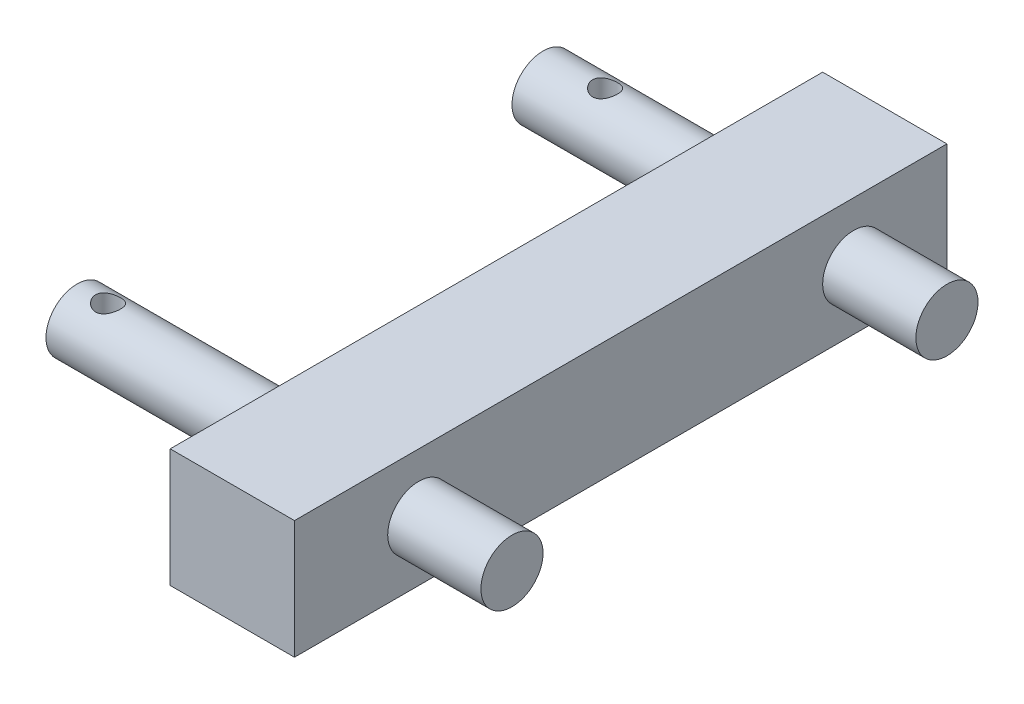
SolidWorks part; units mm, degrees
ref_plane "Front Plane" through (0, 0, 0) normal (0, 0, 1) x (1, 0, 0)
ref_plane "Top Plane" through (0, 0, 0) normal (0, 1, 0) x (1, 0, 0)
ref_plane "Right Plane" through (0, 0, 0) normal (1, 0, 0) x (0, 0, -1)
sketch "Sketch1" plane through (0, 0, 0) normal (1, 0, 0) x (0, 0, -1)
  line L1 (60, 94.9275) -> (-150, 94.9275)
  line L2 (60, 94.9275) -> (60, 56.8275)
  line L3 (60, 56.8275) -> (-150, 56.8275)
  line L4 (-150, 94.9275) -> (-150, 56.8275)
  dimension "D1" = 210
  dimension "D2" = 38.1
extrude "Boss-Extrude1" add sketch "Sketch1" along normal blind 40
sketch "Sketch2" plane through (40, 0, 0) normal (1, 0, 0) x (0, 0, -1)
  line L0 (-150, 56.8275) -> (60, 56.8275) construction
  line L2 (-150, 94.9275) -> (-150, 56.8275) construction
  circle A0 centre (30, 75.8275) radius 10
  dimension "D1" = 180
  dimension "D2" = 20
  dimension "D4" = 19
sketch "Sketch4" plane through (40, 0, 0) normal (1, 0, 0) x (0, 0, -1)
  line L1 (-150, 94.9275) -> (-150, 56.8275) construction
  line L2 (-150, 56.8275) -> (60, 56.8275) construction
  circle A0 centre (-110, 75.8775) radius 10
  dimension "D2" = 20
  dimension "D1" = 40
  dimension "D3" = 19.05
extrude "Boss-Extrude2" add sketch "Sketch4" against normal blind 140 from offset 30
sketch "Sketch5" plane through (0, 0, 0) normal (0, 1, 0) x (1, 0, 0)
  line L0 (-70, -110) -> (0, -110) construction
  line L1 (0, 60) -> (0, -150) construction
  circle A0 centre (-60, -110) radius 4
  dimension "D1" = 8
  dimension "D2" = 60
extrude "Cut-Extrude2" cut sketch "Sketch5" along normal up to next
extrude "Boss-Extrude3" add sketch "Sketch2" against normal blind 130 from offset 30
sketch "Sketch6" plane through (0, 0, 0) normal (0, 1, 0) x (1, 0, 0)
  line L0 (-60, 30) -> (0, 30) construction
  line L1 (0, 60) -> (0, -150) construction
  circle A0 centre (-40, 30) radius 4
  dimension "D1" = 8
  dimension "D2" = 40
extrude "Cut-Extrude3" cut sketch "Sketch6" along normal up to next
